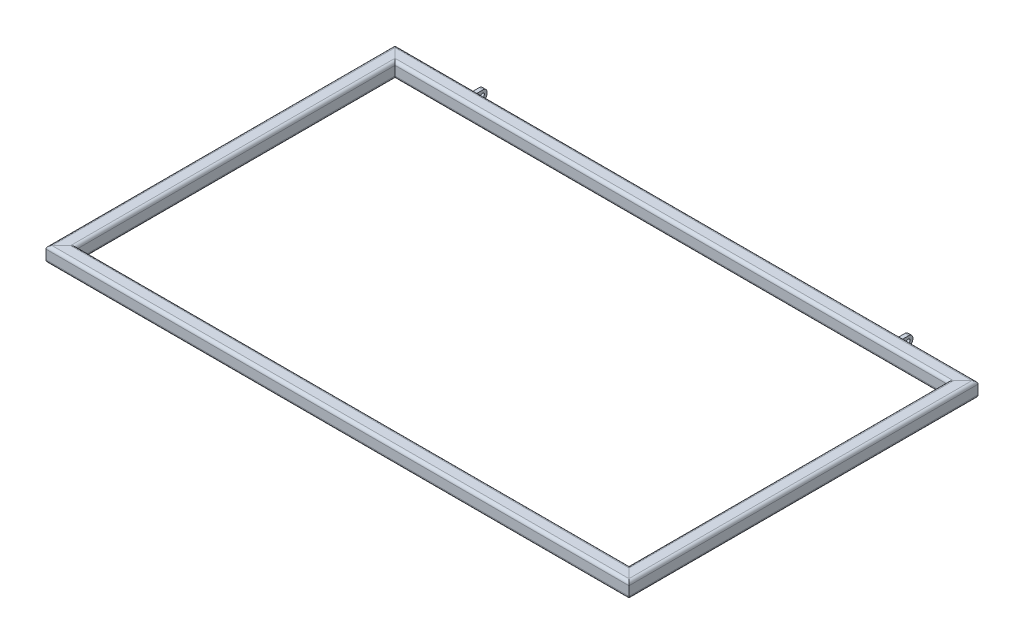
SolidWorks part; units mm, degrees
ref_plane "Front Plane" through (0, 0, 0) normal (0, 0, 1) x (1, 0, 0)
ref_plane "Top Plane" through (0, 0, 0) normal (0, 1, 0) x (1, 0, 0)
ref_plane "Right Plane" through (0, 0, 0) normal (1, 0, 0) x (0, 0, -1)
sketch "Sketch1" plane through (0, 0, 0) normal (0, 1, 0) x (1, 0, 0)
  line L1 (380, -227.5) -> (-380, -227.5)
  line L2 (380, -227.5) -> (380, 227.5)
  line L3 (380, 227.5) -> (-380, 227.5)
  line L4 (-380, -227.5) -> (-380, 227.5)
  line L5 (380, -227.5) -> (-380, 227.5) construction
  line L6 (380, 227.5) -> (-380, -227.5) construction
  point P0 (0, 0)
  dimension "D1" = 455
  dimension "D2" = 760
other "Square tube - configured 20 X 20 X 2(1)"
ref_plane "Plane1" through (380, 0, -217.5) normal (-1, 0, 0) x (0, 0, 1)
sketch "Sketch11" plane through (380, 0, -217.5) normal (-1, 0, 0) x (0, 0, 1)
  line L0 (-6, -8) -> (6, -8)
  line L1 (-8, -6) -> (-8, 6)
  line L2 (6, 8) -> (-6, 8)
  line L3 (8, 6) -> (8, -6)
  line L4 (-6, -10) -> (6, -10)
  line L5 (-10, -6) -> (-10, 6)
  line L6 (6, 10) -> (-6, 10)
  line L7 (10, 6) -> (10, -6)
  arc A0 (10, 6) -> (6, 10) centre (6, 6) ccw
  arc A1 (6, -10) -> (10, -6) centre (6, -6) ccw
  arc A2 (-10, -6) -> (-6, -10) centre (-6, -6) ccw
  arc A3 (-6, 10) -> (-10, 6) centre (-6, 6) ccw
  arc A4 (-6, 8) -> (-8, 6) centre (-6, 6) ccw
  arc A5 (8, 6) -> (6, 8) centre (6, 6) ccw
  arc A6 (6, -8) -> (8, -6) centre (6, -6) ccw
  arc A7 (-8, -6) -> (-6, -8) centre (-6, -6) ccw
  point P0 (-10, 0)
  point P1 (10, 0)
  point P2 (0, 10)
  point P3 (0, -10)
  point P4 (0, 0)
  point P5 (-10, -10)
  point P6 (10, -10)
  point P7 (10, 10)
  point P8 (-10, 10)
  point P33 (0, 0)
  dimension "D1" = 4
  dimension "Thickness" = 2
  dimension "V_leg" = 20
sketch "Sketch12" plane through (0, 0, -227.5) normal (0, 0, -1) x (-1, 0, 0)
  line L0 (380, 6) -> (-380, 6) construction
  line L1 (-280, 6) -> (-275, 6)
  line L2 (-280, 6) -> (-280, -6)
  line L3 (-280, -6) -> (-275, -6)
  line L4 (-275, 6) -> (-275, -6)
  line L5 (380, -6) -> (-380, -6) construction
  line L6 (-380, 6) -> (-380, -6) construction
  line L7 (0, 113.2167) -> (0, -94.2172) construction
  line L8 (275, 6) -> (275, -6)
  line L9 (280, -6) -> (275, -6)
  line L10 (280, 6) -> (280, -6)
  line L11 (280, 6) -> (275, 6)
  dimension "D1" = 5
  dimension "D2" = 100
extrude "Boss-Extrude1" add sketch "Sketch12" along normal blind 15 separate body
fillet "Fillet1" radius 5 2 edges at (277.5, -6, -242.5) (277.5, 6, -242.5)
fillet "Fillet2" radius 5 2 edges at (-277.5, -6, -242.5) (-277.5, 6, -242.5)
sketch "Sketch13" plane through (275, 0, 0) normal (-1, 0, 0) x (0, 0, 1)
  line L0 (-242.5, -1) -> (-242.5, 1) construction
  circle A0 centre (-236.5, 0) radius 2.5
  dimension "D1" = 5
  dimension "D2" = 6
extrude "Cut-Extrude1" cut sketch "Sketch13" against normal through all both and the other way through all
